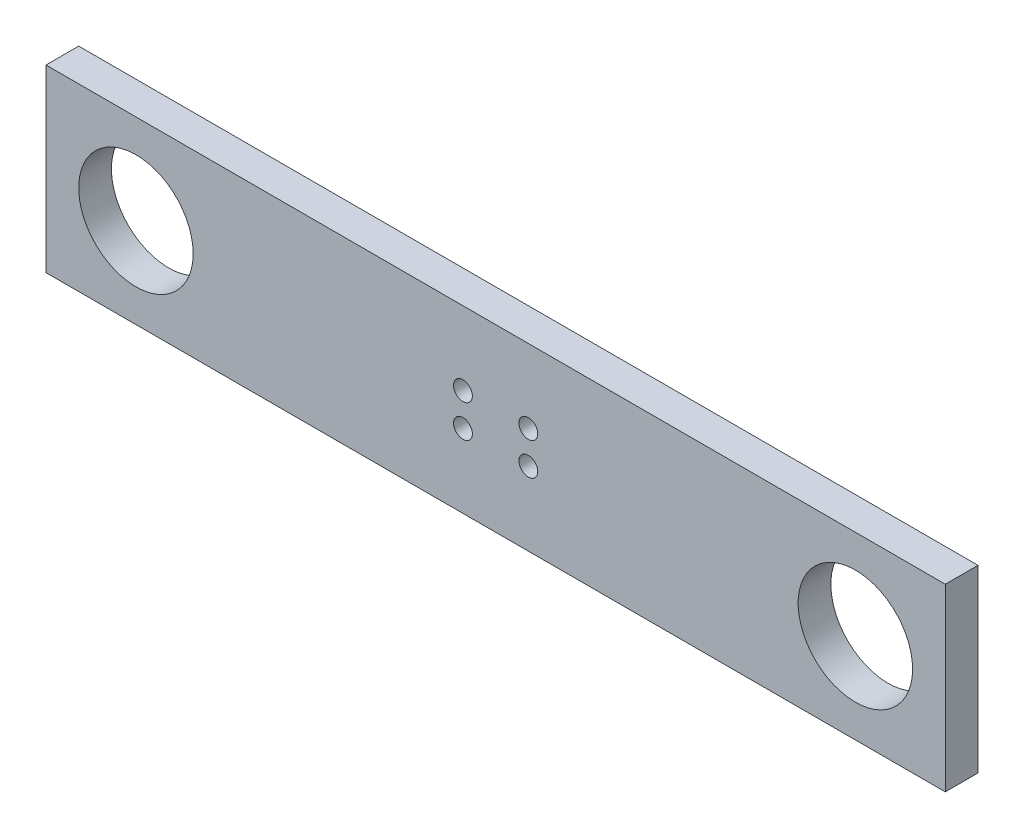
SolidWorks part; units mm, degrees
ref_plane "Front Plane" through (0, 0, 0) normal (0, 0, 1) x (1, 0, 0)
ref_plane "Top Plane" through (0, 0, 0) normal (0, 1, 0) x (1, 0, 0)
ref_plane "Right Plane" through (0, 0, 0) normal (1, 0, 0) x (0, 0, -1)
sketch "Sketch1" plane through (0, 0, 0) normal (0, 0, 1) x (1, 0, 0)
  line L0 (0, 0) -> (69.85, 0) construction
  line L1 (-87.3125, 17.4625) -> (87.3125, 17.4625)
  line L2 (-87.3125, 17.4625) -> (-87.3125, -17.4625)
  line L3 (-87.3125, -17.4625) -> (87.3125, -17.4625)
  line L4 (87.3125, 17.4625) -> (87.3125, -17.4625)
  line L5 (0, 0) -> (-69.85, 0) construction
  line L6 (80.9625, 0) -> (87.3125, 0) construction
  line L7 (69.85, 11.1125) -> (69.85, 17.4625) construction
  line L8 (69.85, -11.1125) -> (69.85, -17.4625) construction
  line L9 (-80.9625, 0) -> (-87.3125, 0) construction
  line L10 (6.35, 3.175) -> (-6.35, -3.175) construction
  line L11 (6.35, 3.175) -> (-6.35, 3.175) construction
  line L12 (6.35, 3.175) -> (6.35, -3.175) construction
  line L13 (6.35, -3.175) -> (-6.35, -3.175) construction
  line L14 (-6.35, 3.175) -> (-6.35, -3.175) construction
  line L15 (6.35, -3.175) -> (-6.35, 3.175) construction
  circle A1 centre (-69.85, 0) radius 11.1125
  circle A2 centre (69.85, 0) radius 11.1125
  circle A3 centre (-6.35, 3.175) radius 1.8288
  circle A4 centre (6.35, 3.175) radius 1.8288
  circle A5 centre (-6.35, -3.175) radius 1.8288
  circle A6 centre (6.35, -3.175) radius 1.8288
  dimension "D1" = 22.225
  dimension "D8" = 3.6576
  dimension "D2" = 6.35
  dimension "D3" = 69.85
  dimension "D5" = 6.35
  dimension "D9" = 12.7
extrude "Boss-Extrude1" add sketch "Sketch1" along normal blind 6.35
